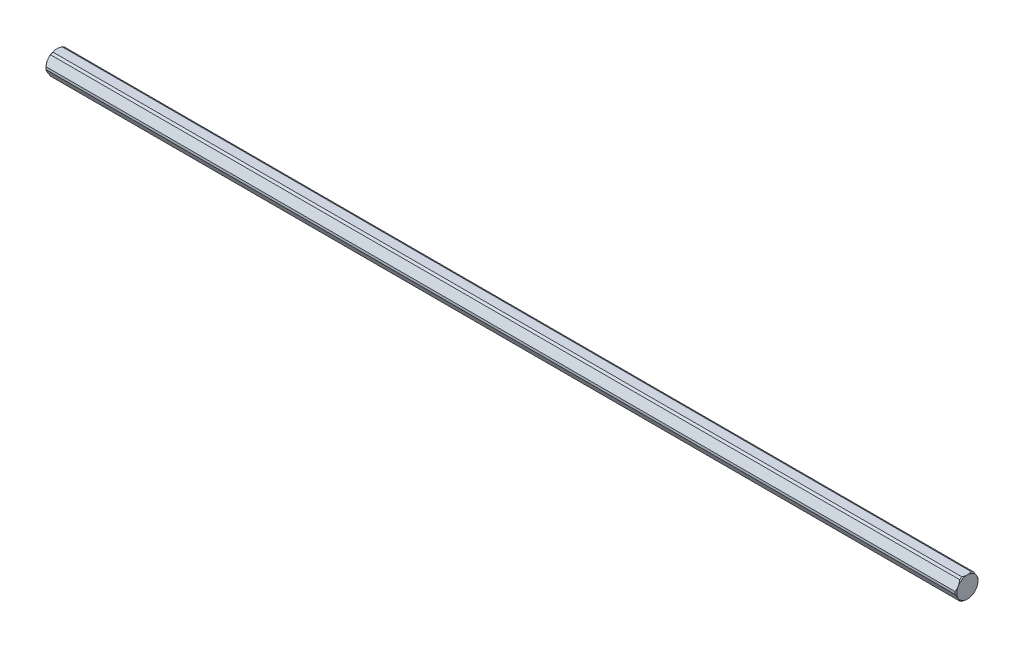
SolidWorks part; units mm, degrees
material "Stainless Steel (ferritic)"
ref_plane "Front Plane" through (0, 0, 0) normal (0, 0, 1) x (1, 0, 0)
ref_plane "Top Plane" through (0, 0, 0) normal (0, 1, 0) x (1, 0, 0)
ref_plane "Right Plane" through (0, 0, 0) normal (1, 0, 0) x (0, 0, -1)
sketch "Sketch1" plane through (0, 0, 0) normal (1, 0, 0) x (0, 0, -1)
  line L0 (-5.9621, 0.6733) -> (-6.3509, 0) construction
  line L1 (2.3979, 5.5) -> (-2.3979, 5.5)
  line L2 (-3.5642, 4.8267) -> (-5.9621, 0.6733)
  line L3 (-5.9621, -0.6733) -> (-3.5642, -4.8267)
  line L4 (-2.3979, -5.5) -> (2.3979, -5.5)
  line L5 (3.5642, -4.8267) -> (5.9621, -0.6733)
  line L6 (5.9621, 0.6733) -> (3.5642, 4.8267)
  line L7 (-6.3509, 0) -> (-5.9621, -0.6733) construction
  line L8 (-3.1754, 5.5) -> (-3.5642, 4.8267) construction
  line L9 (-2.3979, 5.5) -> (-3.1754, 5.5) construction
  line L10 (3.1754, 5.5) -> (2.3979, 5.5) construction
  line L11 (3.5642, 4.8267) -> (3.1754, 5.5) construction
  line L12 (6.3509, 0) -> (5.9621, 0.6733) construction
  line L13 (5.9621, -0.6733) -> (6.3509, 0) construction
  line L14 (3.1754, -5.5) -> (3.5642, -4.8267) construction
  line L15 (2.3979, -5.5) -> (3.1754, -5.5) construction
  line L16 (-3.1754, -5.5) -> (-2.3979, -5.5) construction
  line L17 (-3.5642, -4.8267) -> (-3.1754, -5.5) construction
  circle A0 centre (0, 0) radius 5.5 construction
  arc A1 (-5.9621, 0.6733) -> (-5.9621, -0.6733) centre (0, 0) ccw
  arc A2 (-3.5642, 4.8267) -> (-5.9621, 0.6733) centre (0, 0) ccw construction
  arc A3 (-2.3979, 5.5) -> (-3.5642, 4.8267) centre (0, 0) ccw
  arc A4 (2.3979, 5.5) -> (-2.3979, 5.5) centre (0, 0) ccw construction
  arc A5 (3.5642, 4.8267) -> (2.3979, 5.5) centre (0, 0) ccw
  arc A6 (5.9621, 0.6733) -> (3.5642, 4.8267) centre (0, 0) ccw construction
  arc A7 (5.9621, -0.6733) -> (5.9621, 0.6733) centre (0, 0) ccw
  arc A8 (3.5642, -4.8267) -> (5.9621, -0.6733) centre (0, 0) ccw construction
  arc A9 (2.3979, -5.5) -> (3.5642, -4.8267) centre (0, 0) ccw
  arc A10 (-2.3979, -5.5) -> (2.3979, -5.5) centre (0, 0) ccw construction
  arc A11 (-3.5642, -4.8267) -> (-2.3979, -5.5) centre (0, 0) ccw
  arc A12 (-5.9621, -0.6733) -> (-3.5642, -4.8267) centre (0, 0) ccw construction
  dimension "D2" = 12
  dimension "D1" = 11
extrude "Boss-Extrude1" add sketch "Sketch1" along normal blind 237
sketch "Sketch3" plane through (0, 0, 0) normal (0, 1, 0) x (1, 0, 0)
  line L0 (0, 0) -> (237, 0) construction
  line L2 (236.5, -6) -> (237, -6)
  line L4 (236.5, -6) -> (237, -5.5)
  line L9 (237, -5.5) -> (237, -6)
  line L10 (237, 2.3979) -> (237, -2.3979) construction
  point P5 (237, -5.75)
  dimension "D1" = 237
  dimension "D3" = 6
  dimension "D2" = 45
  dimension "D4" = 0.5
revolve "Cut-Revolve6" cut sketch "Sketch3" angle 360 about L0
mirror "Mirror1" about plane through (0, 0, 0) normal (1, 0, 0) of bodies 102
equation "\"length\"= 474mm"
equation "\"D1@Boss-Extrude1\"=\"length\"/2"
equation "\"D1@Sketch3\"=\"length\"/2"
